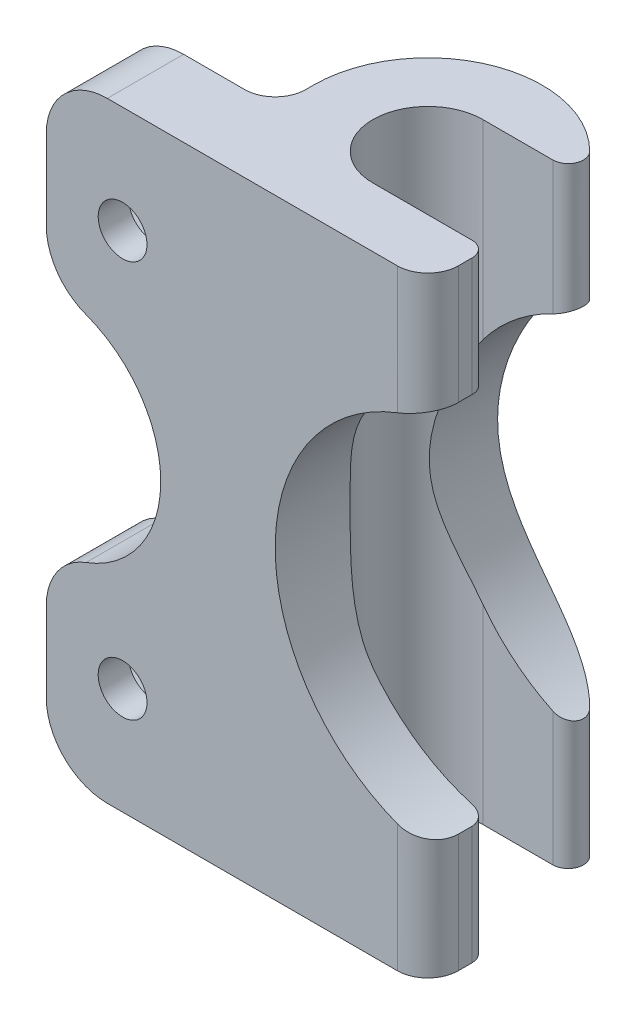
SolidWorks part; units mm, degrees
ref_plane "Alzado" through (0, 0, 0) normal (0, 0, 1) x (1, 0, 0)
ref_plane "Planta" through (0, 0, 0) normal (0, 1, 0) x (1, 0, 0)
ref_plane "Vista lateral" through (0, 0, 0) normal (1, 0, 0) x (0, 0, -1)
sketch "Croquis1" plane through (0, 0, 0) normal (0, 1, 0) x (1, 0, 0)
  line L0 (-17.5, -7.5) -> (7.5, -7.5)
  line L1 (7.5, -7.5) -> (7.5, -3.6)
  line L2 (-7.5, 0) -> (-7.5, -2.5)
  line L3 (-7.5, -2.5) -> (-17.5, -2.5)
  line L4 (-17.5, -2.5) -> (-17.5, -7.5)
  line L5 (0, 3.6) -> (6.5795, 3.6)
  line L6 (0, -3.6) -> (7.5, -3.6)
  arc A0 (0, 3.6) -> (0, -3.6) centre (0, 0) ccw
  arc A1 (6.5795, 3.6) -> (-7.5, 0) centre (0, 0) ccw
  dimension "D1" = 7.2
  dimension "D2" = 15
  dimension "D3" = 25
  dimension "D4" = 5
  dimension "D5" = 10
extrude "Saliente-Extruir1" add sketch "Croquis1" along normal blind 40
sketch "Croquis2" plane through (0, 0, 2.5) normal (0, 0, -1) x (-1, 0, 0)
  line L0 (12.5, 40) -> (12.5, 0) construction
  line L1 (7.5, 40) -> (17.5, 40) construction
  line L2 (7.5, 0) -> (17.5, 0) construction
  line L3 (17.5, 20) -> (7.5, 20) construction
  line L4 (17.5, 40) -> (17.5, 0) construction
  line L5 (7.5, 40) -> (7.5, 0) construction
  circle A0 centre (12.5, 7) radius 1.6
  circle A1 centre (12.5, 33) radius 1.6
  dimension "D1" = 3.2
  dimension "D2" = 13
extrude "Cortar-Extruir1" cut sketch "Croquis2" against normal through all
sketch "Croquis3" plane through (0, 0, 2.5) normal (0, 0, -1) x (-1, 0, 0)
  line L0 (7.5, 20) -> (17.5, 20) construction
  line L1 (15.3, 31.3834) -> (15.3, 34.6166)
  line L2 (15.3, 34.6166) -> (12.5, 36.2332)
  line L3 (12.5, 36.2332) -> (9.7, 34.6166)
  line L4 (9.7, 34.6166) -> (9.7, 31.3834)
  line L5 (9.7, 31.3834) -> (12.5, 29.7668)
  line L6 (12.5, 29.7668) -> (15.3, 31.3834)
  line L7 (7.5, 40) -> (7.5, 0) construction
  line L8 (17.5, 40) -> (17.5, 0) construction
  line L9 (12.5, 10.2332) -> (15.3, 8.6166)
  line L10 (9.7, 8.6166) -> (12.5, 10.2332)
  line L11 (9.7, 5.3834) -> (9.7, 8.6166)
  line L12 (12.5, 3.7668) -> (9.7, 5.3834)
  line L13 (15.3, 5.3834) -> (12.5, 3.7668)
  line L14 (15.3, 8.6166) -> (15.3, 5.3834)
  circle A0 centre (12.5, 33) radius 2.8 construction
  circle A1 centre (12.5, 7) radius 2.8 construction
  dimension "D1" = 5.6
extrude "Cortar-Extruir2" cut sketch "Croquis3" against normal blind 3
sketch "Croquis4" plane through (0, 0, 2.5) normal (0, 0, -1) x (-1, 0, 0)
  line L1 (17.5, 40) -> (17.5, 0) construction
  line L2 (17.5, 20) -> (7.5, 20) construction
  line L3 (7.5, 40) -> (7.5, 0) construction
  line L4 (17.5, 27.5) -> (17.5, 12.5)
  arc A0 (17.5, 27.5) -> (17.5, 12.5) centre (17.5, 20) ccw
  dimension "D1" = 15
extrude "Cortar-Extruir3" cut sketch "Croquis4" against normal through all
fillet "Redondeo1" radius 4 4 edges at (-17.5, 40, 5) (-17.5, 0, 5) (-17.5, 12.5, 5) (-17.5, 27.5, 5)
fillet "Redondeo2" radius 2 2 edges at (7.5, 20, 7.5) (-7.5, 20, 2.5)
fillet "Redondeo3" radius 1 2 edges at (6.5795, 20, -3.6) (7.5, 20, 3.6)
sketch "Croquis5" plane through (0, 0, 0) normal (0, 0, 1) x (1, 0, 0)
  circle A0 centre (10, 20) radius 12.5
  dimension "D2" = 25
  dimension "D1" = 10
  dimension "D3" = 20
extrude "Cortar-Extruir4" cut sketch "Croquis5" against normal through all both and the other way through all
